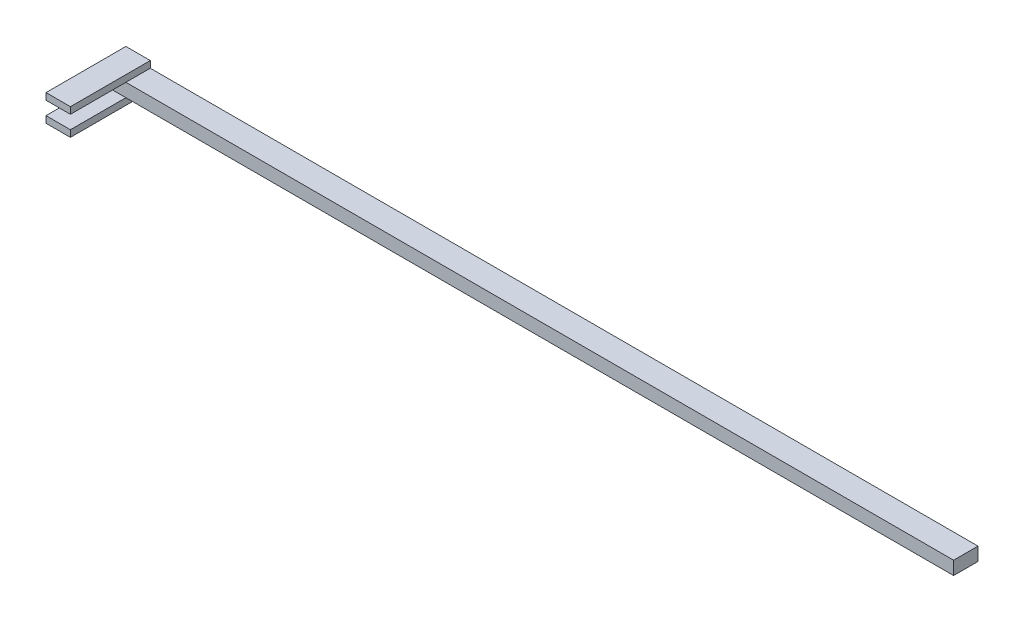
SolidWorks part; units mm, degrees
ref_plane "Front Plane" through (0, 0, 0) normal (0, 0, 1) x (1, 0, 0)
ref_plane "Top Plane" through (0, 0, 0) normal (0, 1, 0) x (1, 0, 0)
ref_plane "Right Plane" through (0, 0, 0) normal (1, 0, 0) x (0, 0, -1)
sketch "Sketch1" plane through (0, 0, 0) normal (0, 1, 0) x (1, 0, 0)
  line L1 (-64.0974, 147.2127) -> (4812.7026, 147.2127)
  line L2 (-64.0974, 147.2127) -> (-64.0974, 7.5127)
  line L3 (-64.0974, 7.5127) -> (4812.7026, 7.5127)
  line L4 (4812.7026, 147.2127) -> (4812.7026, 7.5127)
  dimension "D1" = 139.7
  dimension "D2" = 4876.8
extrude "Boss-Extrude1" add sketch "Sketch1" along normal blind 38.1
sketch "Sketch2" plane through (0, 38.1, 0) normal (0, 1, 0) x (1, 0, 0)
  line L1 (-64.0974, 147.2127) -> (75.6026, 147.2127)
  line L2 (-64.0974, 147.2127) -> (-64.0974, -309.9873)
  line L3 (-64.0974, -309.9873) -> (75.6026, -309.9873)
  line L4 (75.6026, 147.2127) -> (75.6026, -309.9873)
  dimension "D1" = 457.2
  dimension "D2" = 139.7
extrude "Boss-Extrude2" add sketch "Sketch2" along normal blind 38.1
mirror "Mirror1" about plane through (-64.0974, 0, -7.5127) normal (0, 1, 0) of "Boss-Extrude2", "Boss-Extrude1"
